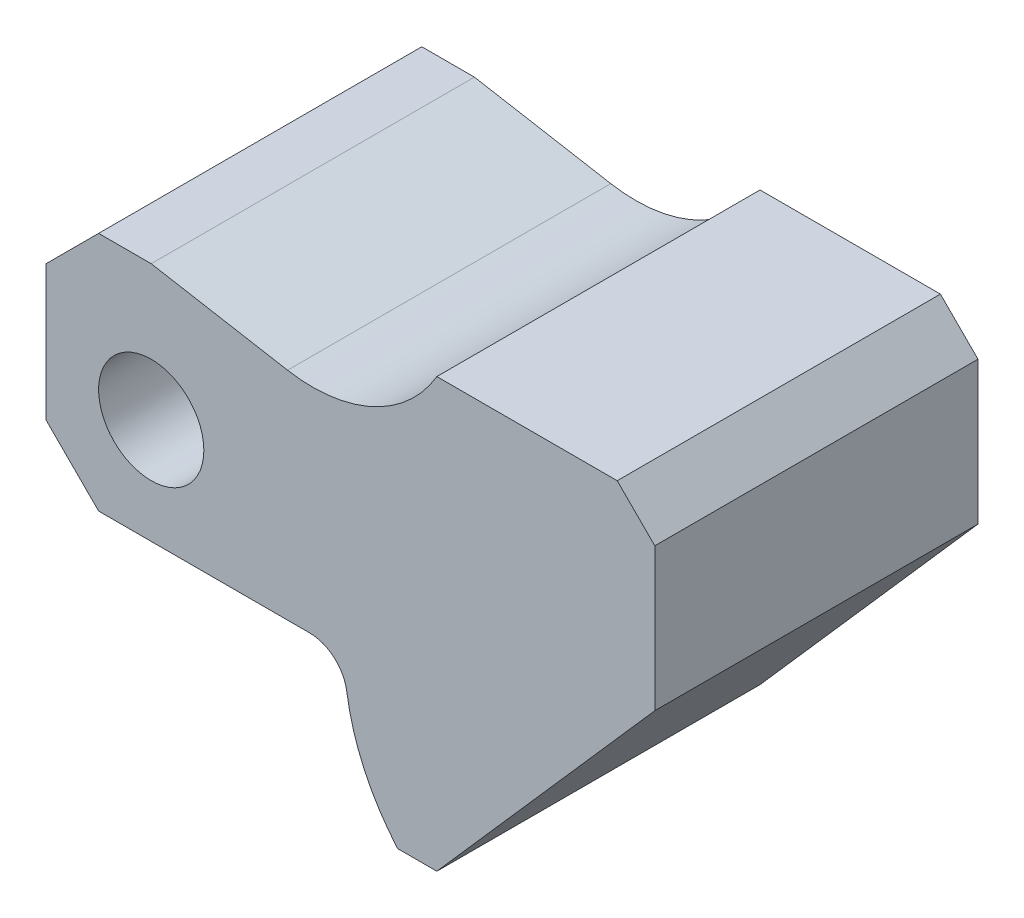
SolidWorks part; units mm, degrees
material "AISI 1020"
ref_plane "Plan de face" through (0, 0, 0) normal (0, 0, 1) x (1, 0, 0)
ref_plane "Plan de dessus" through (0, 0, 0) normal (0, 1, 0) x (1, 0, 0)
ref_plane "Plan de droite" through (0, 0, 0) normal (1, 0, 0) x (0, 0, -1)
sketch "Esquisse2" plane through (0, 0, 0) normal (0, 0, 1) x (1, 0, 0)
  line L0 (46.7881, -19) -> (52, -19)
  line L1 (52, -19) -> (81, 14)
  line L2 (81, 14) -> (81, 33)
  line L3 (76, 38) -> (52, 38)
  line L4 (32.1397, 28.8015) -> (14, 32)
  line L5 (14, 32) -> (7, 32)
  line L6 (0, 25) -> (0, 7)
  line L7 (7, 0) -> (35.0666, 0)
  line L8 (7, 32) -> (0, 25)
  line L9 (0, 7) -> (7, 0)
  line L10 (81, 33) -> (76, 38)
  arc A0 (52, 38) -> (32.1397, 28.8015) centre (35.4651, 47.6608) cw
  arc A1 (35.0666, 0) -> (40.0123, -4.2647) centre (35.0666, -5) cw
  arc A2 (40.0123, -4.2647) -> (46.7881, -19) centre (68.697, 0) ccw
  circle A3 centre (14, 14) radius 7
  point P4 (81, 38)
  point P9 (0, 32)
  point P10 (0, 0)
  point P14 (0, 0)
  point P15 (0, 0)
  dimension "D3" = 29
  dimension "D7" = 19.1503
  dimension "D10" = 5
  dimension "D13" = 14
  dimension "D1" = 81
  dimension "D2" = 57
  dimension "D4" = 29
  dimension "D5" = 24
  dimension "D6" = 14
  dimension "D8" = 10
  dimension "D9" = 32
  dimension "D11" = 14
  dimension "D12" = 14
  dimension "D14" = 19
  dimension "D15" = 29
  dimension "D16" = 19
  dimension "D17" = 7
  dimension "D18" = 45
  dimension "D19" = 7
  dimension "D20" = 45
  dimension "D21" = 5
  dimension "D22" = 45
extrude "Boss.-Extru.2" add sketch "Esquisse2" along normal mid plane 43
equation "\"A\"= 81"
equation "\"B\"= 57"
equation "\"C\"= 43"
